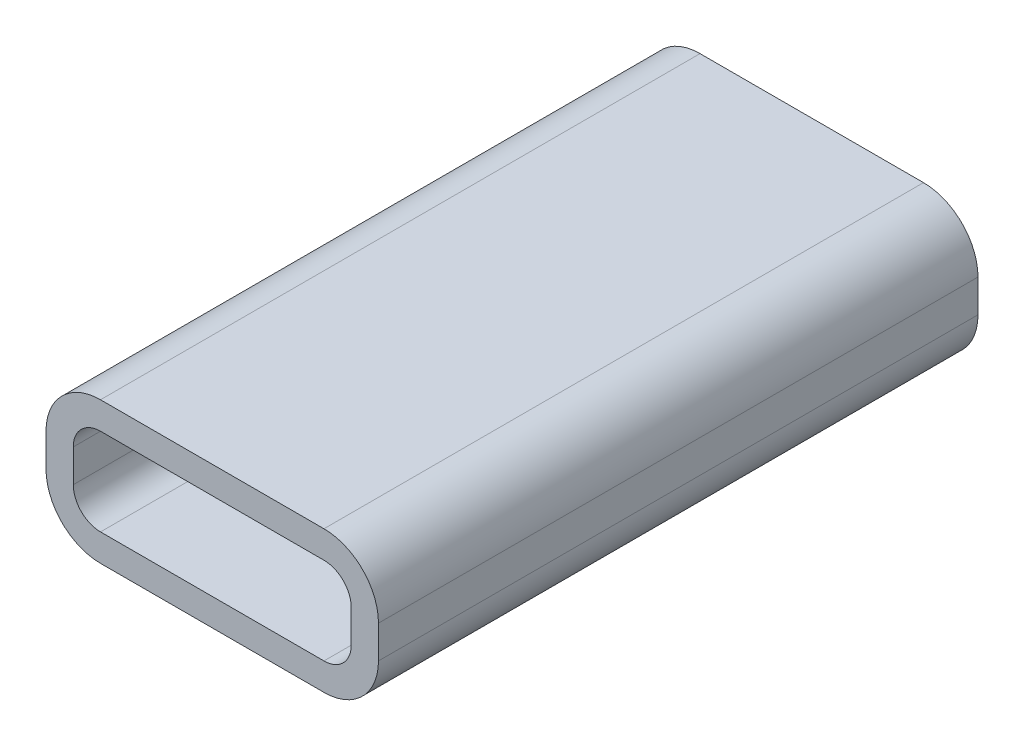
SolidWorks part; units mm, degrees
ref_plane "Plan de face" through (0, 0, 0) normal (0, 0, 1) x (1, 0, 0)
ref_plane "Plan de dessus" through (0, 0, 0) normal (0, 1, 0) x (1, 0, 0)
ref_plane "Plan de droite" through (0, 0, 0) normal (1, 0, 0) x (0, 0, -1)
sketch "Esquisse1" plane through (0, 0, 0) normal (0, 0, 1) x (1, 0, 0)
  line L0 (-4.1, 1.6) -> (4.1, 1.6)
  line L1 (5.1, 0.6) -> (5.1, -0.6)
  line L2 (4.1, -1.6) -> (-4.1, -1.6)
  line L3 (-5.1, -0.6) -> (-5.1, 0.6)
  line L4 (-4.1, 2.6) -> (4.1, 2.6)
  line L5 (6.1, 0.6) -> (6.1, -0.6)
  line L6 (4.1, -2.6) -> (-4.1, -2.6)
  line L7 (-6.1, -0.6) -> (-6.1, 0.6)
  arc A0 (-4.1, -1.6) -> (-5.1, -0.6) centre (-4.1, -0.6) cw
  arc A1 (5.1, -0.6) -> (4.1, -1.6) centre (4.1, -0.6) cw
  arc A2 (4.1, 1.6) -> (5.1, 0.6) centre (4.1, 0.6) cw
  arc A3 (-4.1, 1.6) -> (-5.1, 0.6) centre (-4.1, 0.6) ccw
  arc A4 (4.1, 2.6) -> (6.1, 0.6) centre (4.1, 0.6) cw
  arc A5 (6.1, -0.6) -> (4.1, -2.6) centre (4.1, -0.6) cw
  arc A6 (-4.1, -2.6) -> (-6.1, -0.6) centre (-4.1, -0.6) cw
  arc A7 (-4.1, 2.6) -> (-6.1, 0.6) centre (-4.1, 0.6) ccw
  point P6 (-5.1, -1.6)
  point P11 (5.1, 1.6)
  point P14 (-5.1, 1.6)
  point P15 (0, 1.6)
  point P16 (-5.1, 0)
  dimension "D3" = 1
  dimension "D1" = 3.2
  dimension "D2" = 10.2
  dimension "D4" = 1
extrude "Boss.-Extru.2" add sketch "Esquisse1" along normal blind 10
sketch "Esquisse2" plane through (0, 0, 0) normal (0, 0, -1) x (-1, 0, 0)
  line L4 (4.1, 2.6) -> (-4.1, 2.6)
  line L5 (-6.1, 0.6) -> (-6.1, -0.6)
  line L6 (-4.1, -2.6) -> (4.1, -2.6)
  line L7 (6.1, -0.6) -> (6.1, 0.6)
  line L8 (4.1, 2.6) -> (-4.1, 2.6)
  line L9 (-6.1, 0.6) -> (-6.1, -0.6)
  line L10 (-4.1, -2.6) -> (4.1, -2.6)
  line L11 (6.1, -0.6) -> (6.1, 0.6)
  arc A4 (6.1, 0.6) -> (4.1, 2.6) centre (4.1, 0.6) ccw
  arc A5 (-4.1, 2.6) -> (-6.1, 0.6) centre (-4.1, 0.6) ccw
  arc A6 (-6.1, -0.6) -> (-4.1, -2.6) centre (-4.1, -0.6) ccw
  arc A7 (4.1, -2.6) -> (6.1, -0.6) centre (4.1, -0.6) ccw
  arc A8 (6.1, 0.6) -> (4.1, 2.6) centre (4.1, 0.6) ccw
  arc A9 (-4.1, 2.6) -> (-6.1, 0.6) centre (-4.1, 0.6) ccw
  arc A10 (-6.1, -0.6) -> (-4.1, -2.6) centre (-4.1, -0.6) ccw
  arc A11 (4.1, -2.6) -> (6.1, -0.6) centre (4.1, -0.6) ccw
  dimension "D1" = 0
extrude "Boss.-Extru.3" add sketch "Esquisse2" along normal blind 1
mirror "Symétrie1" about plane through (-4.1, 0.6, -1) normal (0, 0, -1) of "Boss.-Extru.2", "Boss.-Extru.3"
